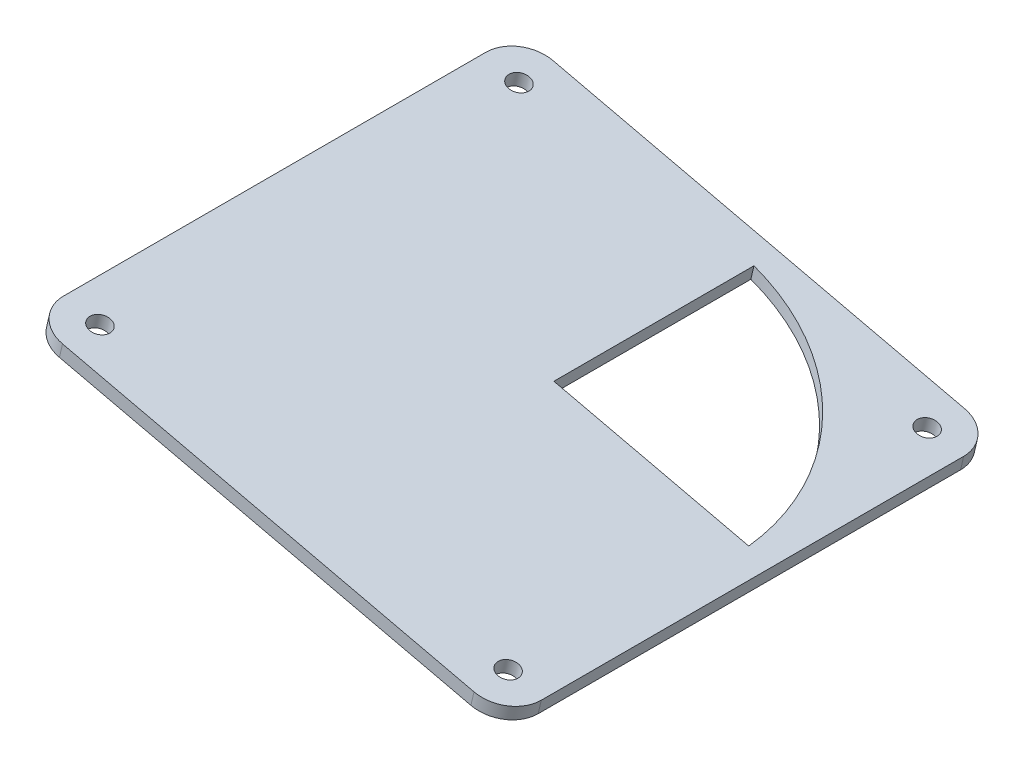
SolidWorks part; units mm, degrees
material "PET"
ref_plane "Front Plane" through (0, 0, 0) normal (0, 0, 1) x (1, 0, 0)
ref_plane "Top Plane" through (0, 0, 0) normal (0, 1, 0) x (1, 0, 0)
ref_plane "Right Plane" through (0, 0, 0) normal (1, 0, 0) x (0, 0, -1)
sketch "Sketch1" plane through (12.9103, 55.5764, 0) normal (0.2263, 0.9741, 0) x (0.9741, -0.2263, 0)
  line L1 (-65.4218, -70.2764) -> (-3.4218, -70.2764)
  line L2 (-70.4218, -65.2764) -> (-70.4218, -3.2764)
  line L3 (-65.4218, 1.7236) -> (-3.4218, 1.7236)
  line L4 (1.5782, -65.2764) -> (1.5782, -3.2764)
  line L5 (-70.4218, -70.2764) -> (1.5782, 1.7236) construction
  line L6 (-70.4218, 1.7236) -> (1.5782, -70.2764) construction
  circle A0 centre (-65.1718, -3.5264) radius 1.5
  circle A1 centre (-65.1718, -65.0264) radius 1.5
  circle A2 centre (-3.6718, -65.0264) radius 1.5
  circle A3 centre (-3.6718, -3.5264) radius 1.5
  circle A4 centre (-34.4218, -34.2764) radius 32.5
  arc A5 (-65.4218, -70.2764) -> (-70.4218, -65.2764) centre (-65.4218, -65.2764) cw
  arc A6 (-3.4218, -70.2764) -> (1.5782, -65.2764) centre (-3.4218, -65.2764) ccw
  arc A7 (-3.4218, 1.7236) -> (1.5782, -3.2764) centre (-3.4218, -3.2764) cw
  arc A8 (-70.4218, -3.2764) -> (-65.4218, 1.7236) centre (-65.4218, -3.2764) cw
  dimension "D1" = 65
  dimension "D4" = 5
  dimension "D2" = 72
  dimension "D3" = 72
extrude "Boss-Extrude1" add sketch "Sketch1" along normal blind 2
sketch "Sketch2" plane through (13.3629, 57.5245, 0) normal (0.2263, 0.9741, 0) x (0.9741, -0.2263, 0)
  line L0 (-34.4218, -51.7764) -> (-34.4218, -1.7764)
  line L1 (-66.9218, -34.2764) -> (-1.9218, -34.2764)
  line L2 (-31.4218, -51.7764) -> (-31.4218, -1.7764)
  line L3 (-37.4218, -51.7764) -> (-37.4218, -1.7764)
  line L4 (-66.9218, -37.2764) -> (-1.9218, -37.2764)
  line L5 (-66.9218, -31.2764) -> (-1.9218, -31.2764)
  circle A0 centre (-34.4218, -34.2764) radius 32.5 construction
  circle A3 centre (-34.4218, -34.2764) radius 32.5
  circle A4 centre (-34.4218, -34.2764) radius 32.5
  point P9 (0, 0)
  point P14 (-34.4218, -34.2764)
  circle M17 centre (-34.4218, -34.2764) radius 32.5
  dimension "D1" = 3
  dimension "D2" = 3
  dimension "D3" = 3
  dimension "D4" = 3
  dimension "D5" = 0
extrude "Boss-Extrude2" add sketch "Sketch2" against normal blind 2 contours L5 L1 L3 M17 | L4 L3 L1 M17 | L3 L5 L0 M17 | L0 L5 L2 M17 | L5 L2 L1 M17 | L2 L4 L1 M17 | L5 L0 L1 L2 | L5 L3 L1 L0 | L3 L4 L0 L1 | L0 L4 L2 L1 | L4 L0 L2 M17 | L4 L3 L0 M17
